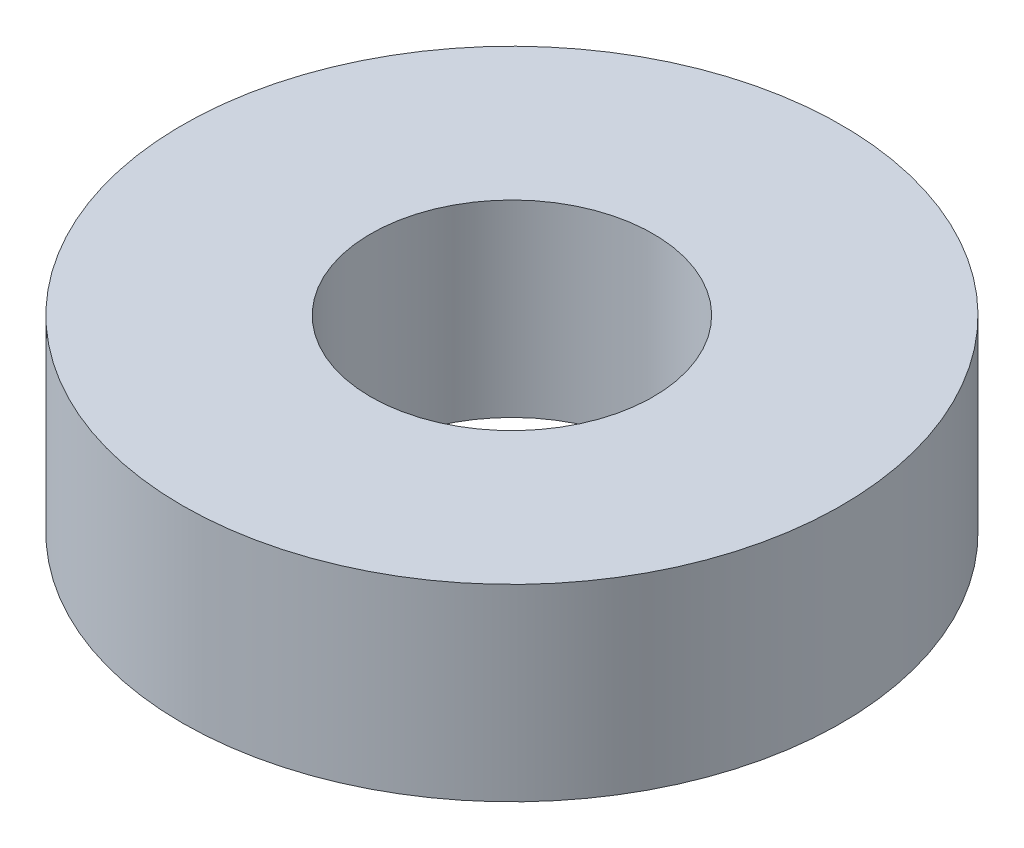
SolidWorks part; units mm, degrees
ref_plane "Front Plane" through (0, 0, 0) normal (0, 0, 1) x (1, 0, 0)
ref_plane "Top Plane" through (0, 0, 0) normal (0, 1, 0) x (1, 0, 0)
ref_plane "Right Plane" through (0, 0, 0) normal (1, 0, 0) x (0, 0, -1)
sketch "Sketch1" plane through (0, 0, 0) normal (0, 1, 0) x (1, 0, 0)
  circle A0 centre (0, 0) radius 0.875
  circle A1 centre (0, 0) radius 0.375
  dimension "D1" = 1.75
  dimension "D2" = 0.75
extrude "Boss-Extrude2" add sketch "Sketch1" along normal blind 0.5
